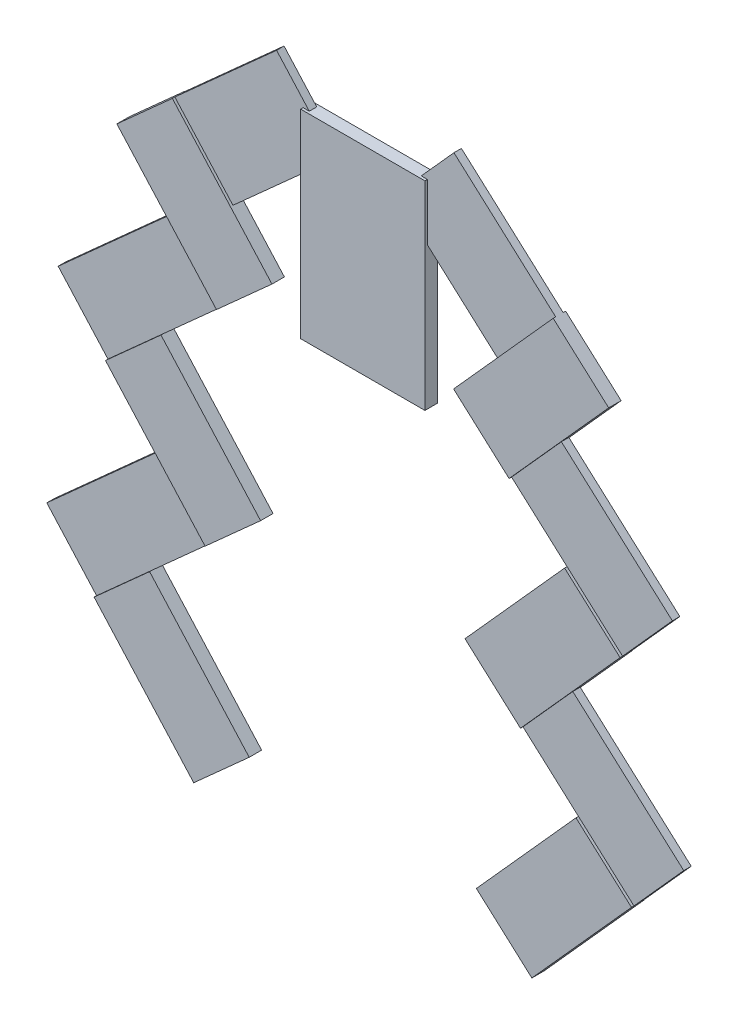
SolidWorks part; units mm, degrees
ref_plane "Front Plane" through (0, 0, 0) normal (0, 0, 1) x (1, 0, 0)
ref_plane "Top Plane" through (0, 0, 0) normal (0, 1, 0) x (1, 0, 0)
ref_plane "Right Plane" through (0, 0, 0) normal (1, 0, 0) x (0, 0, -1)
sketch "Sketch1" plane through (0, 0, 0) normal (0, 0, 1) x (1, 0, 0)
  line L1 (0, 0) -> (-127, 0)
  line L2 (0, 0) -> (0, 203.2)
  line L3 (0, 203.2) -> (-127, 203.2)
  line L4 (-127, 0) -> (-127, 203.2)
  dimension "D1" = 127
  dimension "D2" = 203.2
extrude "Boss-Extrude1" add sketch "Sketch1" along normal blind 12.7
ref_plane "Plane1" through (0, 0, 6.35) normal (0, 0, 1) x (1, 0, 0)
sketch "Sketch2" plane through (0, 0, 6.35) normal (0, 0, 1) x (1, 0, 0)
  line L3 (-94.7468, 174.2487) -> (-198.7174, 80.9417)
  line L4 (-198.7174, 80.9417) -> (-258.0946, 147.1049)
  line L5 (-32.2532, 174.2487) -> (71.7174, 80.9417)
  line L6 (-32.2532, 174.2487) -> (27.124, 240.4118)
  line L7 (71.7174, 80.9417) -> (131.0946, 147.1049)
  line L8 (27.124, 240.4118) -> (131.0946, 147.1049)
  line L9 (-154.124, 240.4118) -> (-258.0946, 147.1049)
  line L10 (-94.7468, 174.2487) -> (-154.124, 240.4118)
  dimension "D1" = 88.9
  dimension "D2" = 139.7
extrude "Boss-Extrude2" add sketch "Sketch2" along normal blind 3.81 and the other way blind 3.81 separate body
sketch "Sketch3" plane through (0, 0, 10.16) normal (0, 0, 1) x (1, 0, 0)
  line L1 (-258.0946, 147.1049) -> (-156.3052, 33.6823)
  line L2 (-258.0946, 147.1049) -> (-314.8059, 96.2101)
  line L3 (-156.3052, 33.6823) -> (-213.0164, -17.2124)
  line L4 (-314.8059, 96.2101) -> (-213.0164, -17.2124)
  line L6 (29.3052, 33.6823) -> (86.0164, -17.2124)
  line L7 (187.8059, 96.2101) -> (86.0164, -17.2124)
  line L8 (131.0946, 147.1049) -> (29.3052, 33.6823)
  line L9 (131.0946, 147.1049) -> (187.8059, 96.2101)
  dimension "D1" = 152.4
  dimension "D2" = 76.2
extrude "Boss-Extrude3" add sketch "Sketch3" along normal up to surface and the other way up to surface
ref_plane "Plane2" through (0, 0, 6.35) normal (0, 0, 1) x (1, 0, 0)
sketch "Sketch4" plane through (0, 0, 6.35) normal (0, 0, 1) x (1, 0, 0)
  line L0 (-213.0164, -17.2124) -> (-263.9112, 39.4989)
  line L1 (-213.0164, -17.2124) -> (-326.439, -119.0018)
  line L2 (-263.9112, 39.4989) -> (-377.3337, -62.2906)
  line L3 (-326.439, -119.0018) -> (-377.3337, -62.2906)
  line L4 (-314.8059, 96.2101) -> (-213.0164, -17.2124) construction
  line L7 (199.439, -119.0018) -> (250.3337, -62.2906)
  line L8 (136.9112, 39.4989) -> (250.3337, -62.2906)
  line L9 (86.0164, -17.2124) -> (136.9112, 39.4989)
  line L10 (86.0164, -17.2124) -> (199.439, -119.0018)
  dimension "D1" = 152.4
extrude "Boss-Extrude4" add sketch "Sketch4" along normal blind 3.81 and the other way blind 3.81
sketch "Sketch5" plane through (0, 0, 10.16) normal (0, 0, 1) x (1, 0, 0)
  line L0 (-326.439, -119.0018) -> (-269.7277, -68.1071)
  line L1 (-326.439, -119.0018) -> (-224.6495, -232.4244)
  line L2 (-269.7277, -68.1071) -> (-167.9383, -181.5296)
  line L3 (-224.6495, -232.4244) -> (-167.9383, -181.5296)
  line L4 (-326.439, -119.0018) -> (-213.0164, -17.2124) construction
  line L7 (97.6495, -232.4244) -> (40.9383, -181.5296)
  line L8 (199.439, -119.0018) -> (97.6495, -232.4244)
  line L9 (199.439, -119.0018) -> (142.7277, -68.1071)
  line L10 (142.7277, -68.1071) -> (40.9383, -181.5296)
  dimension "D1" = 152.4
extrude "Boss-Extrude5" add sketch "Sketch5" along normal up to surface and the other way up to surface
sketch "Sketch6" plane through (0, 0, 6.35) normal (0, 0, 1) x (1, 0, 0)
  line L0 (-224.6495, -232.4244) -> (-275.5442, -175.7131)
  line L1 (-224.6495, -232.4244) -> (-338.072, -334.2138)
  line L2 (-275.5442, -175.7131) -> (-388.9668, -277.5025)
  line L3 (-338.072, -334.2138) -> (-388.9668, -277.5025)
  line L4 (-326.439, -119.0018) -> (-224.6495, -232.4244) construction
  line L7 (211.072, -334.2138) -> (261.9668, -277.5025)
  line L8 (148.5442, -175.7131) -> (261.9668, -277.5025)
  line L9 (97.6495, -232.4244) -> (211.072, -334.2138)
  line L10 (97.6495, -232.4244) -> (148.5442, -175.7131)
  dimension "D1" = 152.4
extrude "Boss-Extrude6" add sketch "Sketch6" along normal blind 3.81 and the other way blind 3.81
sketch "Sketch7" plane through (0, 0, 10.16) normal (0, 0, 1) x (1, 0, 0)
  line L0 (-338.072, -334.2138) -> (-281.3608, -283.3191)
  line L1 (-338.072, -334.2138) -> (-236.2826, -447.6363)
  line L2 (-281.3608, -283.3191) -> (-179.5713, -396.7416)
  line L3 (-236.2826, -447.6363) -> (-179.5713, -396.7416)
  line L4 (-338.072, -334.2138) -> (-224.6495, -232.4244) construction
  line L5 (211.072, -334.2138) -> (154.3608, -283.3191)
  line L6 (211.072, -334.2138) -> (109.2826, -447.6363)
  line L7 (154.3608, -283.3191) -> (52.5713, -396.7416)
  line L8 (109.2826, -447.6363) -> (52.5713, -396.7416)
  line L9 (97.6495, -232.4244) -> (211.072, -334.2138) construction
  dimension "D1" = 152.4
  dimension "D2" = 152.4
extrude "Boss-Extrude7" add sketch "Sketch7" along normal up to surface and the other way up to surface
